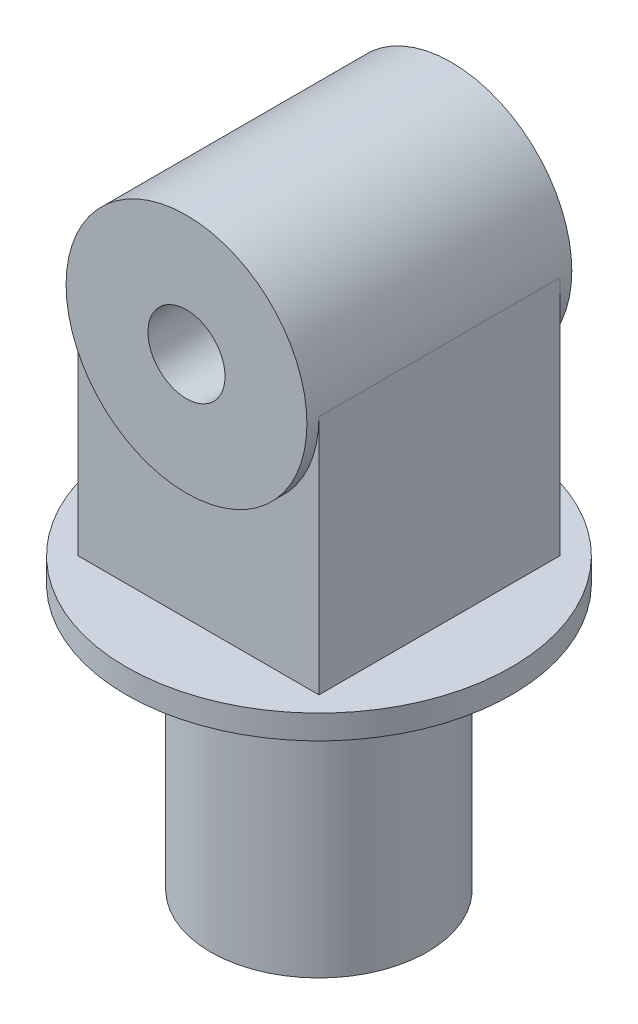
SolidWorks part; units mm, degrees
ref_plane "Ön Düzlem" through (0, 0, 0) normal (0, 0, 1) x (1, 0, 0)
ref_plane "Üst Düzlem" through (0, 0, 0) normal (0, 1, 0) x (1, 0, 0)
ref_plane "Sağ Düzlem" through (0, 0, 0) normal (1, 0, 0) x (0, 0, -1)
sketch "Çizim1" plane through (0, 0, 0) normal (0, 1, 0) x (1, 0, 0)
  circle A0 centre (0, 0) radius 22.5
  dimension "D1" = 45
extrude "Yükseklik-Ekstrüzyon1" add sketch "Çizim1" along normal blind 60
sketch "Çizim2" plane through (0, 60, 0) normal (0, 1, 0) x (1, 0, 0)
  circle A0 centre (0, 0) radius 22.5
  circle A1 centre (0, 0) radius 40
  dimension "D1" = 80
  dimension "D2" = 45
extrude "Yükseklik-Ekstrüzyon2" add sketch "Çizim2" against normal blind 5
sketch "Çizim3" plane through (0, 60, 0) normal (0, 1, 0) x (1, 0, 0)
  line L1 (-25, -25) -> (25, -25)
  line L2 (-25, -25) -> (-25, 25)
  line L3 (-25, 25) -> (25, 25)
  line L4 (25, -25) -> (25, 25)
  line L5 (-25, -25) -> (25, 25) construction
  line L6 (-25, 25) -> (25, -25) construction
  point P0 (0, 0)
  dimension "D1" = 50
extrude "Yükseklik-Ekstrüzyon3" add sketch "Çizim3" along normal blind 50
sketch "Çizim4" plane through (0, 0, 0) normal (0, 0, 1) x (1, 0, 0)
  line L0 (-25, 110) -> (25, 110) construction
  circle A0 centre (0, 110) radius 25
extrude "Yükseklik-Ekstrüzyon4" add sketch "Çizim4" along normal mid plane 55
sketch "Çizim5" plane through (0, 0, 27.5) normal (0, 0, 1) x (1, 0, 0)
  circle A0 centre (0, 110) radius 8
  dimension "D1" = 16
extrude "Kes-Ekstrüzyon1" cut sketch "Çizim5" against normal through all
